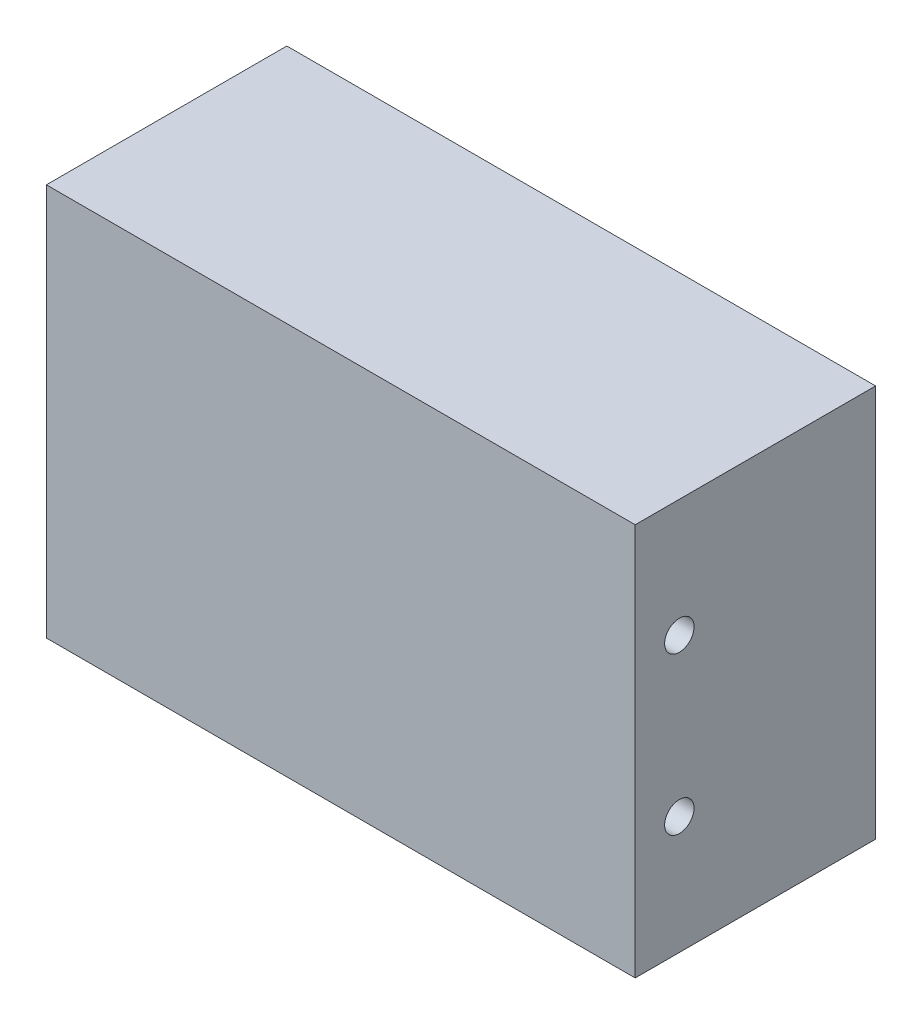
SolidWorks part; units mm, degrees
ref_plane "前视基准面" through (0, 0, 0) normal (0, 0, 1) x (1, 0, 0)
ref_plane "上视基准面" through (0, 0, 0) normal (0, 1, 0) x (1, 0, 0)
ref_plane "右视基准面" through (0, 0, 0) normal (1, 0, 0) x (0, 0, -1)
sketch "草图1" plane through (0, 0, 0) normal (0, 1, 0) x (1, 0, 0)
  line L1 (-30, -12.25) -> (30, -12.25)
  line L2 (-30, -12.25) -> (-30, 12.25)
  line L3 (-30, 12.25) -> (30, 12.25)
  line L4 (30, -12.25) -> (30, 12.25)
  line L5 (-30, -12.25) -> (30, 12.25) construction
  line L6 (-30, 12.25) -> (30, -12.25) construction
  point P0 (0, 0)
  dimension "D1" = 24.5
  dimension "D2" = 60
extrude "凸台-拉伸1" add sketch "草图1" along normal blind 40
sketch "草图2" plane through (0, 0, 0) normal (0, -1, 0) x (-1, 0, 0)
  line L0 (0, 0) -> (0, -7.75) construction
  line L1 (8, -7.75) -> (-8, -7.75) construction
  line L2 (30, -12.25) -> (-30, -12.25) construction
  circle A0 centre (8, -7.75) radius 1.5
  circle A1 centre (-8, -7.75) radius 1.5
  point P6 (0, -7.75)
  dimension "D3" = 3
  dimension "D1" = 4.5
  dimension "D2" = 16
extrude "切除-拉伸1" cut sketch "草图2" against normal blind 0.5
sketch "草图3" plane through (30, 0, 0) normal (1, 0, 0) x (0, 0, -1)
  line L0 (-12.25, 20) -> (-7.75, 20) construction
  line L1 (-12.25, 40) -> (-12.25, 0) construction
  line L2 (-7.75, 28) -> (-7.75, 12) construction
  circle A0 centre (-7.75, 28) radius 1.5
  circle A1 centre (-7.75, 12) radius 1.5
  point P7 (-7.75, 20)
  dimension "D3" = 3
  dimension "D1" = 4.5
  dimension "D2" = 16
extrude "切除-拉伸2" cut sketch "草图3" against normal blind 3
